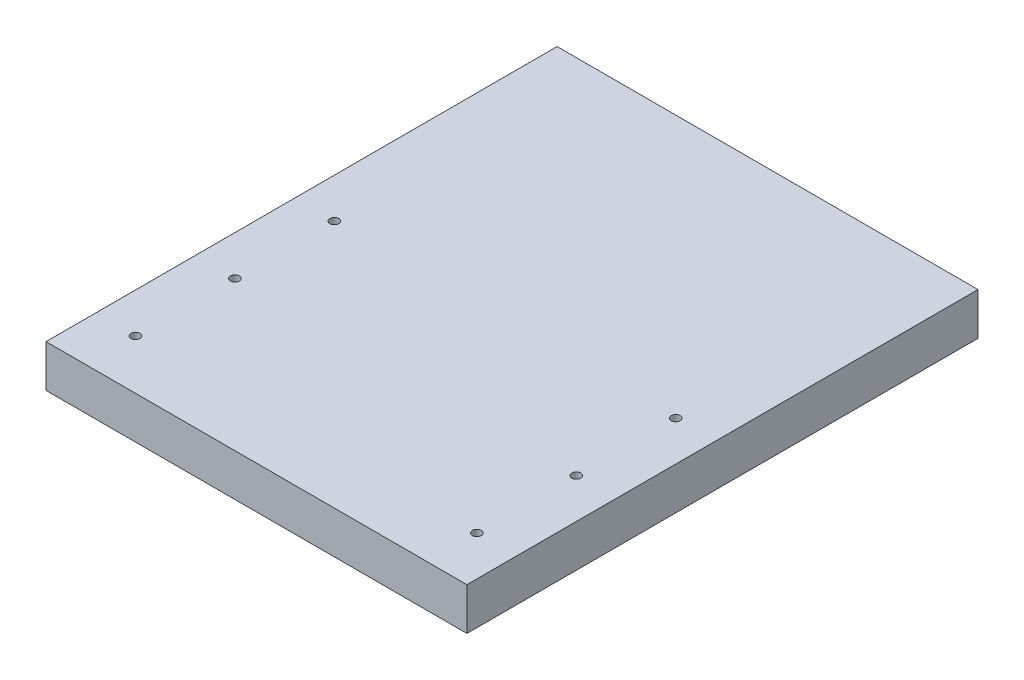
SolidWorks part; units mm, degrees
ref_plane "Front Plane" through (0, 0, 0) normal (0, 0, 1) x (1, 0, 0)
ref_plane "Top Plane" through (0, 0, 0) normal (0, 1, 0) x (1, 0, 0)
ref_plane "Right Plane" through (0, 0, 0) normal (1, 0, 0) x (0, 0, -1)
sketch "Sketch1" plane through (0, 0, 0) normal (0, 1, 0) x (1, 0, 0)
  line L1 (0, 0) -> (127, 0)
  line L2 (0, 0) -> (0, 154.21)
  line L3 (0, 154.21) -> (127, 154.21)
  line L4 (127, 0) -> (127, 154.21)
extrude "Boss-Extrude1" add sketch "Sketch1" along normal blind 12.75
ref_plane "Plane1" through (63.5, 0, 0) normal (-1, 0, 0) x (0, 0, 1)
sketch "Sketch2" plane through (0, 12.75, 0) normal (0, 1, 0) x (1, 0, 0)
  line L0 (12, 0) -> (12, 154.21) construction
  line L1 (0, 0) -> (127, 0) construction
  line L2 (127, 154.21) -> (0, 154.21) construction
  line L3 (12, 77.105) -> (115, 77.105) construction
  line L4 (115, 0) -> (115, 154.21) construction
  line L5 (12, 36.47) -> (0, 36.47) construction
  line L6 (0, 154.21) -> (0, 0) construction
  line L7 (0, 15) -> (127, 15) construction
  line L8 (127, 0) -> (127, 154.21) construction
  line L10 (0, 45) -> (127, 45) construction
  line L12 (0, 75) -> (127, 75) construction
  circle A0 centre (12, 15) radius 1.35
  circle A1 centre (115, 15) radius 1.35
  circle A2 centre (115, 45) radius 1.35
  circle A3 centre (12, 45) radius 1.35
  circle A4 centre (12, 75) radius 1.35
  circle A5 centre (115, 75) radius 1.35
extrude "Cut-Extrude1" cut sketch "Sketch2" against normal through all
